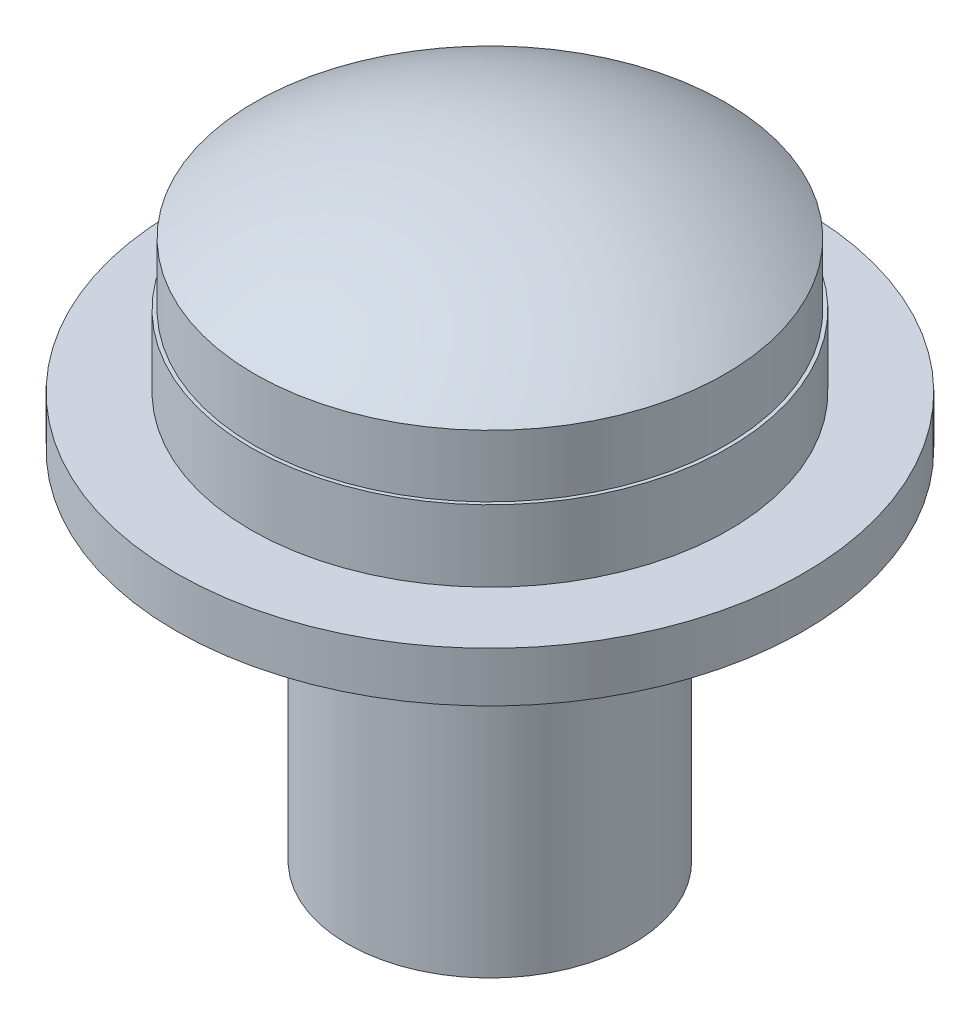
SolidWorks part; units mm, degrees
other "标注1"
sketch "草图7" plane through (4.4, 5.6, 4.4) normal (0.6477, 0.4057, 0.6449) x (0.605, 0.2405, -0.759)
other "细节项目1"
ref_plane "前视基准面" through (0, 0, 0) normal (0, 0, 1) x (1, 0, 0)
ref_plane "上视基准面" through (0, 0, 0) normal (0, 1, 0) x (1, 0, 0)
ref_plane "右视基准面" through (0, 0, 0) normal (1, 0, 0) x (0, 0, -1)
sketch "草图1" plane through (0, 0, 0) normal (0, 1, 0) x (1, 0, 0)
  circle A0 centre (0, 0) radius 4.4
  dimension "D1" = 8.8
extrude "凸台-拉伸1" add sketch "草图1" along normal blind 0.7
sketch "草图2" plane through (0, 0.7, 0) normal (0, 1, 0) x (1, 0, 0)
  circle A0 centre (0, 0) radius 3.35
  dimension "D1" = 6.7
extrude "凸台-拉伸2" add sketch "草图2" along normal blind 1
sketch "草图3" plane through (0, 1.7, 0) normal (0, 1, 0) x (1, 0, 0)
  circle A0 centre (0, 0) radius 3.4
  dimension "D1" = 6.8
extrude "凸台-拉伸3" add sketch "草图3" along normal blind 1.9
sketch "草图4" plane through (0, 1.7, 0) normal (0, -1, 0) x (1, 0, 0)
  circle A0 centre (0, 0) radius 3.3
  circle A1 centre (0, 0) radius 10.5263
  dimension "D1" = 6.6
extrude "切除-拉伸1" cut sketch "草图4" against normal blind 1
sketch "草图6" plane through (0, 0, 0) normal (0, -1, 0) x (1, 0, 0)
  circle A0 centre (0, 0) radius 2
  dimension "D1" = 4
extrude "凸台-拉伸4" add sketch "草图6" along normal blind 5
sketch "草图8" plane through (0, 0, 0) normal (1, 0, 0) x (0, 0, -1)
  line L0 (3.4, 3.6) -> (-3.4, 3.6) construction
  line L1 (0, 3.6) -> (0, -7.9915)
  line L4 (0, 3.6) -> (0, 4.6874)
  line L5 (0, 4.6874) -> (5.6063, 4.6874)
  line L6 (5.6063, 4.6874) -> (5.6063, -0.7259)
  arc A0 (0, -7.9915) -> (0, 3.6) centre (0, -2.1957) ccw
  point P1 (0, -6.8484)
  point P10 (0, -2.1957)
revolve "切除-旋转3" cut sketch "草图8" angle 360 about L1
